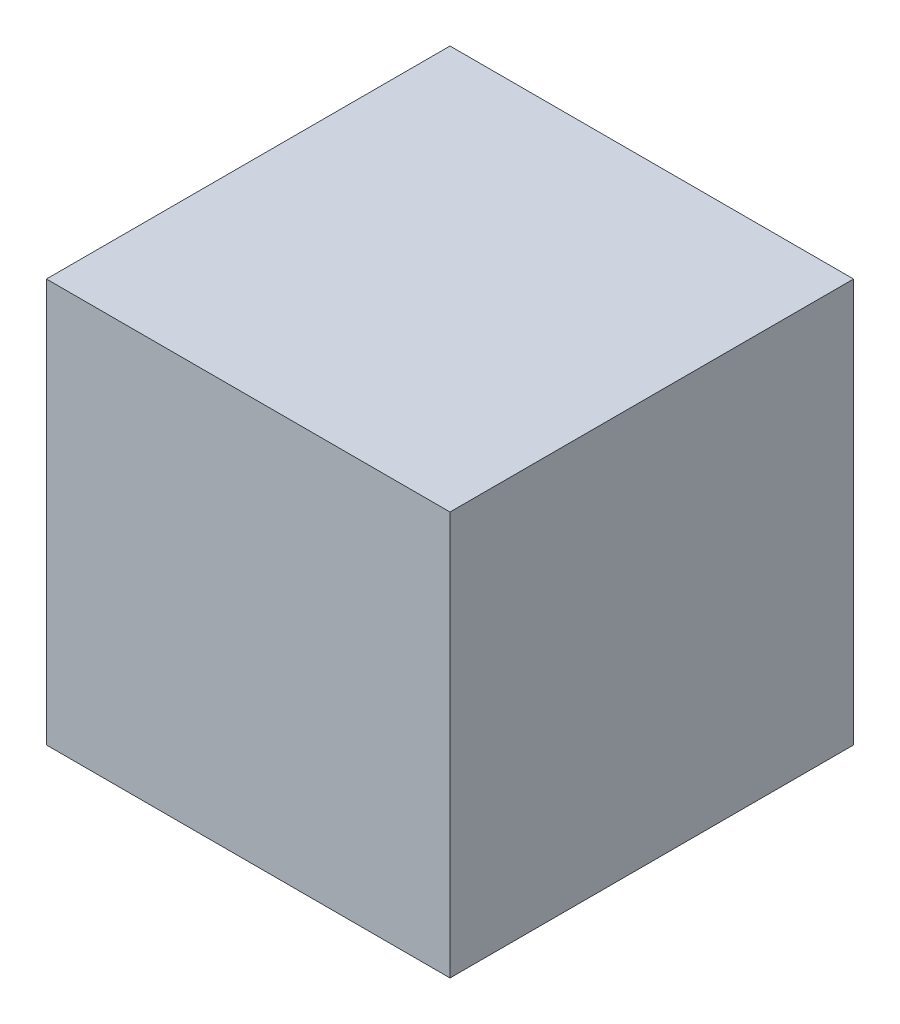
SolidWorks part; units mm, degrees
ref_plane "Front Plane" through (0, 0, 0) normal (0, 0, 1) x (1, 0, 0)
ref_plane "Top Plane" through (0, 0, 0) normal (0, 1, 0) x (1, 0, 0)
ref_plane "Right Plane" through (0, 0, 0) normal (1, 0, 0) x (0, 0, -1)
sketch "Sketch1" plane through (0, 0, 0) normal (0, 0, 1) x (1, 0, 0)
  line L0 (-53.3677, 4.6234) -> (-53.3677, 14.6234)
  line L1 (-53.3677, 14.6234) -> (-43.3677, 14.6234)
  line L2 (-43.3677, 14.6234) -> (-43.3677, 4.6234)
  line L3 (-43.3677, 4.6234) -> (-53.3677, 4.6234)
extrude "Boss-Extrude1" add sketch "Sketch1" along normal blind 10
